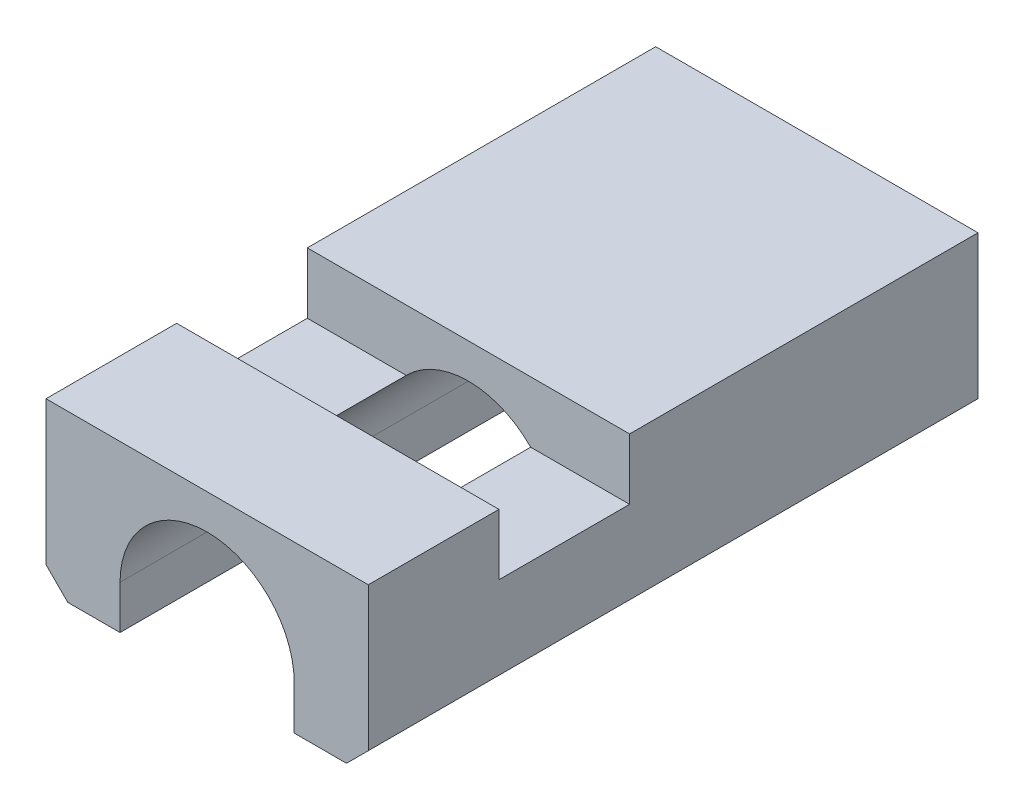
SolidWorks part; units mm, degrees
ref_plane "Front Plane" through (0, 0, 0) normal (0, 0, 1) x (1, 0, 0)
ref_plane "Top Plane" through (0, 0, 0) normal (0, 1, 0) x (1, 0, 0)
ref_plane "Right Plane" through (0, 0, 0) normal (1, 0, 0) x (0, 0, -1)
sketch "Sketch1" plane through (0, 0, 0) normal (0, 0, 1) x (1, 0, 0)
  line L0 (-23.1713, 58.5489) -> (-23.1713, 56.5489) construction
  line L1 (-26.8713, 53.7489) -> (-26.8713, 52.7489)
  line L2 (-26.8713, 53.7489) -> (-19.4713, 53.7489) construction
  line L3 (-26.8713, 53.7489) -> (-26.8713, 56.5489)
  line L4 (-26.8713, 56.5489) -> (-19.4713, 56.5489)
  line L5 (-19.4713, 53.7489) -> (-19.4713, 56.5489)
  line L6 (-26.8713, 52.7489) -> (-25.1713, 52.7489)
  line L7 (-25.1713, 52.7489) -> (-25.1713, 53.7489)
  line L8 (-21.1713, 53.7489) -> (-21.1713, 52.7489)
  line L9 (-21.1713, 52.7489) -> (-19.4713, 52.7489)
  line L10 (-19.4713, 52.7489) -> (-19.4713, 53.7489)
  line L11 (-23.1713, 56.5489) -> (-23.1713, 53.7489) construction
  circle A1 centre (-23.1713, 53.7489) radius 3.7 construction
  circle A2 centre (-23.1713, 53.7489) radius 2 construction
  arc A3 (-25.1713, 53.7489) -> (-21.1713, 53.7489) centre (-23.1713, 53.7489) cw
  point P0 (0, 0)
  dimension "D1" = 7.4
  dimension "D2" = 4
  dimension "D3" = 2
  dimension "D4" = 2.8
  dimension "D5" = 1
extrude "Boss-Extrude1" add sketch "Sketch1" along normal blind 14
chamfer "Chamfer1" distance 0.5 angle 45 2 edges at (-19.4713, 52.7489, 7) (-26.8713, 52.7489, 7)
sketch "Sketch2" plane through (-19.4713, 0, 0) normal (1, 0, 0) x (0, 0, -1)
  line L0 (-14, 56.5489) -> (0, 56.5489) construction
  line L1 (-11, 56.5489) -> (-8, 56.5489)
  line L2 (-11, 56.5489) -> (-11, 55.1489)
  line L3 (-11, 55.1489) -> (-8, 55.1489)
  line L4 (-8, 56.5489) -> (-8, 55.1489)
  line L5 (-11, 55.8489) -> (-14, 55.8489) construction
  line L6 (-14, 53.2489) -> (-14, 56.5489) construction
  dimension "D1" = 1.4
  dimension "D2" = 3
  dimension "D3" = 3
extrude "Cut-Extrude1" cut sketch "Sketch2" against normal blind 15
